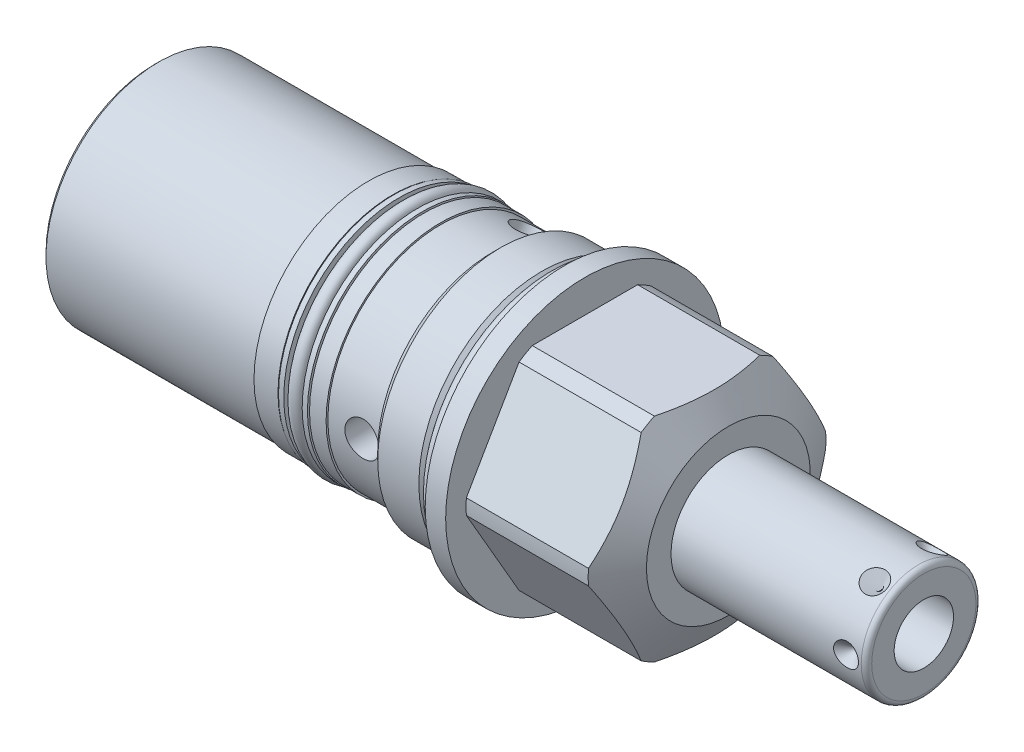
SolidWorks part; units mm, degrees
material "Alloy Steel"
ref_plane "Front Plane" through (0, 0, 0) normal (0, 0, 1) x (1, 0, 0)
ref_plane "Top Plane" through (0, 0, 0) normal (0, 1, 0) x (1, 0, 0)
ref_plane "Right Plane" through (0, 0, 0) normal (1, 0, 0) x (0, 0, -1)
sketch "Sketch1" plane through (0, 0, 0) normal (0, 0, 1) x (1, 0, 0)
  line L0 (0, 0) -> (113.8544, 0) construction
  line L1 (0, 26.9875) -> (3.9624, 26.9875)
  line L2 (3.9624, 26.9875) -> (3.9624, 23.0251)
  line L3 (3.9624, 23.0251) -> (27.6219, 23.0251)
  line L4 (27.6219, 23.0251) -> (31.75, 15.875)
  line L5 (31.75, 15.875) -> (31.75, 0)
  line L6 (31.75, 0) -> (-79.375, 0)
  line L7 (-79.375, 0) -> (-79.375, 21.844)
  line L8 (0, 26.9875) -> (0, 22.3012)
  line L9 (0, 22.3012) -> (-2.8956, 22.3012)
  line L10 (-2.8956, 22.3012) -> (-4.4069, 23.8125)
  line L11 (-4.4069, 23.8125) -> (-12.3698, 23.8125)
  line L12 (-12.3698, 23.8125) -> (-13.9954, 22.1869)
  line L14 (-13.9954, 22.1869) -> (-13.9954, 21.844)
  line L15 (-13.9954, 21.844) -> (-79.375, 21.844)
  dimension "D1" = 53.975
  dimension "D2" = 31.75
  dimension "D3" = 3.9624
  dimension "D4" = 31.75
  dimension "D5" = 46.0502
  dimension "D6" = 30
  dimension "D7" = 79.375
  dimension "D8" = 76.4794
  dimension "D9" = 44.6024
  dimension "D10" = 45
  dimension "D11" = 47.625
  dimension "D12" = 11.0998
  dimension "D13" = 44.3738
  dimension "D14" = 43.688
revolve "Revolve1" add sketch "Sketch1" angle 360 about L0
sketch "Sketch2" plane through (31.75, 0, 0) normal (1, 0, 0) x (0, 0, -1)
  line L1 (11.9151, 20.6375) -> (-11.9151, 20.6375)
  line L2 (-11.9151, 20.6375) -> (-23.8301, 0)
  line L3 (-23.8301, 0) -> (-11.9151, -20.6375)
  line L4 (-11.9151, -20.6375) -> (11.9151, -20.6375)
  line L5 (11.9151, -20.6375) -> (23.8301, 0)
  line L6 (23.8301, 0) -> (11.9151, 20.6375)
  circle A0 centre (0, 0) radius 20.6375 construction
  dimension "D1" = 41.275
extrude "Cut-Extrude1" cut sketch "Sketch2" against normal up to surface (27.7876 mm away) flip side to cut up to face at (3.9624, 0, 26.9875)
sketch "Sketch3" plane through (0, 0, 0) normal (0, 0, 1) x (1, 0, 0)
  line L0 (0, 0) -> (52.5154, 0) construction
  line L1 (31.75, 11.1125) -> (68.6054, 11.1125)
  line L2 (31.75, -15.875) -> (31.75, 15.875) construction
  line L3 (69.6214, 10.0965) -> (69.6214, 0)
  line L4 (69.6214, 0) -> (31.75, 0)
  line L5 (31.75, 0) -> (31.75, 11.1125)
  line L6 (0, 26.9875) -> (0, -26.9875) construction
  arc A0 (69.6214, 10.0965) -> (68.6054, 11.1125) centre (68.6054, 10.0965) ccw
  dimension "D1" = 1.016
  dimension "D2" = 69.6214
  dimension "D3" = 22.225
revolve "Revolve2" add sketch "Sketch3" angle 360 about L0
sketch "Sketch4" plane through (0, 0, 0) normal (0, 1, 0) x (1, 0, 0)
  line L0 (65.659, 10.0738) -> (65.659, 0) construction
  line L1 (69.6214, -10.0965) -> (69.6214, 10.0965) construction
  line L2 (68.072, 11.1125) -> (65.659, 11.1125)
  line L3 (68.6054, 11.1125) -> (31.75, 11.1125) construction
  line L4 (65.659, 11.1125) -> (65.659, 8.6995)
  line L5 (65.659, 8.6995) -> (68.072, 11.1125)
  dimension "D1" = 3.9624
  dimension "D2" = 45
  dimension "D3" = 4.826
revolve "Cut-Revolve1" cut sketch "Sketch4" angle 360 about L0
pattern_circular "CirPattern1" count 6 over 360 about axis through (0, 0, 0) along (-1, 0, 0) of "Cut-Revolve1"
sketch "Sketch5" plane through (0, 0, 0) normal (0, 0, 1) x (1, 0, 0)
  line L0 (0, 0) -> (44.9273, 0) construction
  line L1 (69.6214, 5.7531) -> (52.6034, 5.7531)
  line L2 (69.6214, -10.0965) -> (69.6214, 10.0965) construction
  line L3 (52.6034, 5.7531) -> (49.1466, 0)
  line L4 (49.1466, 0) -> (69.6214, 0)
  line L5 (69.6214, 0) -> (69.6214, 5.7531)
  dimension "D1" = 17.018
  dimension "D2" = 59
  dimension "D3" = 11.5062
revolve "Cut-Revolve2" cut sketch "Sketch5" angle 360 about L0
sketch "Sketch6" plane through (0, 0, 0) normal (0, 0, 1) x (1, 0, 0)
  line L0 (-24.003, 21.844) -> (-24.003, 22.1869)
  line L1 (-13.9954, 21.844) -> (-79.375, 21.844) construction
  line L2 (-24.003, 22.1869) -> (-37.973, 22.1869)
  line L3 (-37.973, 22.1869) -> (-37.973, 21.844)
  line L4 (-37.973, 21.844) -> (-24.003, 21.844)
  line L5 (0, 0) -> (-62.9111, 0) construction
  line L6 (-79.375, 21.844) -> (-79.375, -21.844) construction
  dimension "D1" = 13.97
  dimension "D2" = 44.3738
  dimension "D3" = 41.402
revolve "Revolve3" add sketch "Sketch6" angle 360 about L5
sketch "Sketch7" plane through (-79.375, 0, 0) normal (-1, 0, 0) x (0, 0, 1)
  circle A0 centre (0, 0) radius 3.1369
  dimension "D1" = 6.2738
extrude "Cut-Extrude2" cut sketch "Sketch7" against normal blind 0.762
sketch "Sketch8" plane through (0, 0, 0) normal (0, 0, 1) x (1, 0, 0)
  line L0 (0, 0) -> (-56.7277, 0) construction
  line L1 (-24.003, 22.1869) -> (-37.973, 22.1869) construction
  line L2 (-33.3248, 22.1869) -> (-27.2161, 22.1869)
  line L3 (-33.3248, 22.1869) -> (-33.3248, 20.1549)
  line L4 (-33.3248, 20.1549) -> (-27.2161, 20.1549)
  line L5 (-27.2161, 22.1869) -> (-27.2161, 20.1549)
  line L6 (-79.375, 21.844) -> (-79.375, -21.844) construction
  dimension "D1" = 6.1087
  dimension "D2" = 46.0502
  dimension "D3" = 40.3098
revolve "Cut-Revolve3" cut sketch "Sketch8" angle 360 about L0
sketch "Sketch9" plane through (0, 0, 0) normal (0, 0, 1) x (1, 0, 0)
  line L0 (0, 0) -> (-59.2046, 0) construction
  line L1 (-30.2705, 14.9069) -> (-30.2705, -14.8344) construction
  line L2 (-33.3248, -22.1869) -> (-33.3248, 22.1869) construction
  line L3 (-27.2161, 20.1549) -> (-27.2161, -20.1549) construction
  line L4 (-27.2161, 20.1549) -> (-33.3248, 20.1549) construction
  line L5 (-28.4861, 22.3393) -> (-27.4701, 22.3393)
  line L6 (-28.4861, 22.3393) -> (-28.4861, 20.1549)
  line L7 (-28.4861, 20.1549) -> (-27.4701, 20.1549)
  line L8 (-27.4701, 22.3393) -> (-27.4701, 20.1549)
  line L9 (-27.2161, 22.1869) -> (-27.2161, -22.1869) construction
  line L10 (-33.0708, 22.3393) -> (-33.0708, 20.1549)
  line L11 (-32.0548, 20.1549) -> (-33.0708, 20.1549)
  line L12 (-32.0548, 22.3393) -> (-32.0548, 20.1549)
  line L13 (-32.0548, 22.3393) -> (-33.0708, 22.3393)
  dimension "D1" = 1.016
  dimension "D2" = 0.254
  dimension "D3" = 2.1844
revolve "Revolve4" add sketch "Sketch9" angle 360 about L0
sketch "Sketch10" plane through (0, 0, 0) normal (0, 1, 0) x (1, 0, 0)
  line L0 (-17.399, 23.0369) -> (-17.399, -3.4735) construction
  line L1 (-79.375, 21.844) -> (-79.375, -21.844) construction
  line L2 (-17.399, -23.8125) -> (-20.7137, -23.8125)
  line L4 (-20.7137, -23.8125) -> (-20.7137, -11.1125)
  line L5 (-20.7137, -11.1125) -> (-17.399, -11.1125)
  line L6 (-17.399, -11.1125) -> (-17.399, -23.8125)
  line L8 (-12.3698, -23.8125) -> (-4.4069, -23.8125) construction
  dimension "D1" = 61.976
  dimension "D2" = 6.6294
  dimension "D3" = 11.1125
revolve "Cut-Revolve4" cut sketch "Sketch10" angle 360 about L0
pattern_circular "CirPattern2" count 3 over 360 about axis through (0, 0, 0) along (1, 0, 0) of "Cut-Revolve4"
chamfer "Chamfer1" distance 0.762 angle 45 1 edges at (-79.375, 0, 21.844)
sketch "Sketch11" plane through (0, 0, 0) normal (0, 0, 1) x (1, 0, 0)
  line L0 (0, 0) -> (23.6366, 0) construction
  line L1 (0, 26.9875) -> (0, -26.9875) construction
  line L2 (0, 22.3012) -> (-2.8956, 22.3012) construction
  circle A0 centre (-1.4732, 23.7744) radius 1.4732
  dimension "D1" = 2.9464
  dimension "D2" = 47.5488
revolve "Revolve5" add sketch "Sketch11" angle 360 about L0
sketch "Sketch12" plane through (0, 0, 0) normal (0, 0, 1) x (1, 0, 0)
  line L0 (0, 0) -> (-56.0967, 0) construction
  line L1 (-28.4861, 20.1549) -> (-32.0548, 20.1549) construction
  line L2 (-30.2704, 21.463) -> (-30.2704, 6.0377) construction
  line L3 (-33.3248, -22.1869) -> (-33.3248, 22.1869) construction
  line L4 (-27.2161, 20.1549) -> (-27.2161, -20.1549) construction
  circle A0 centre (-30.2704, 21.463) radius 1.3081
  dimension "D1" = 2.6162
revolve "Revolve7" add sketch "Sketch12" angle 360 about L0
sketch "Sketch13" plane through (-79.375, 0, 0) normal (-1, 0, 0) x (0, 0, 1)
  circle A0 centre (0, 0) radius 17.7927
extrude "Extrude1" add sketch "Sketch13" along normal blind 0.508
sketch "Sketch14" plane through (-79.883, 0, 0) normal (-1, 0, 0) x (0, 0, 1)
  circle A0 centre (0, 0) radius 3.1369
extrude "Cut-Extrude4" cut sketch "Sketch14" against normal blind 0.508
